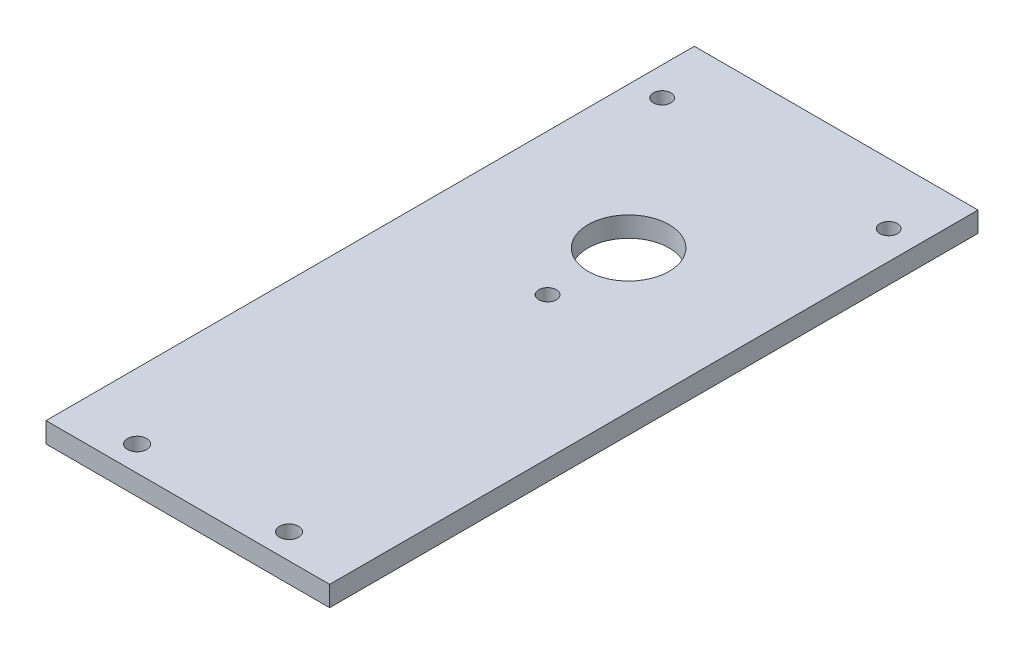
SolidWorks part; units mm, degrees
ref_plane "Front Plane" through (0, 0, 0) normal (0, 0, 1) x (1, 0, 0)
ref_plane "Top Plane" through (0, 0, 0) normal (0, 1, 0) x (1, 0, 0)
ref_plane "Right Plane" through (0, 0, 0) normal (1, 0, 0) x (0, 0, -1)
sketch "Sketch1" plane through (0, 0, 0) normal (0, 1, 0) x (1, 0, 0)
  line L1 (0, 0) -> (88.9, 0)
  line L2 (0, 0) -> (0, 203.2)
  line L3 (0, 203.2) -> (88.9, 203.2)
  line L4 (88.9, 0) -> (88.9, 203.2)
  dimension "D1" = 88.9
  dimension "D2" = 203.2
extrude "Boss-Extrude1" add sketch "Sketch1" along normal blind 6.35
ref_plane "Plane1" through (44.45, 0, 0) normal (1, 0, 0) x (0, 0, -1)
sketch "Sketch2" plane through (0, 0, 0) normal (0, -1, 0) x (1, 0, 0)
  line L0 (8.95, -184.15) -> (79.95, -184.15) construction
  line L1 (88.9, -203.2) -> (0, -203.2) construction
  line L2 (88.9, 0) -> (88.9, -203.2) construction
  circle A0 centre (20.6375, -7.9135) radius 3
  circle A1 centre (68.2625, -7.9135) radius 3
  circle A2 centre (44.45, -112.75) radius 2.75
  circle A3 centre (8.95, -184.15) radius 2.75
  circle A4 centre (79.95, -184.15) radius 2.75
  circle A5 centre (44.45, -138.15) radius 12.7
  point P12 (44.45, -184.15)
  dimension "D1" = 6
  dimension "D2" = 6
  dimension "D3" = 5.5
  dimension "D4" = 5.5
  dimension "D5" = 5.5
  dimension "D8" = 25.4
  dimension "D6" = 71
  dimension "D7" = 71.4
  dimension "D9" = 25.4
  dimension "D10" = 19.05
  dimension "D11" = 44.45
extrude "Cut-Extrude1" cut sketch "Sketch2" against normal through all
